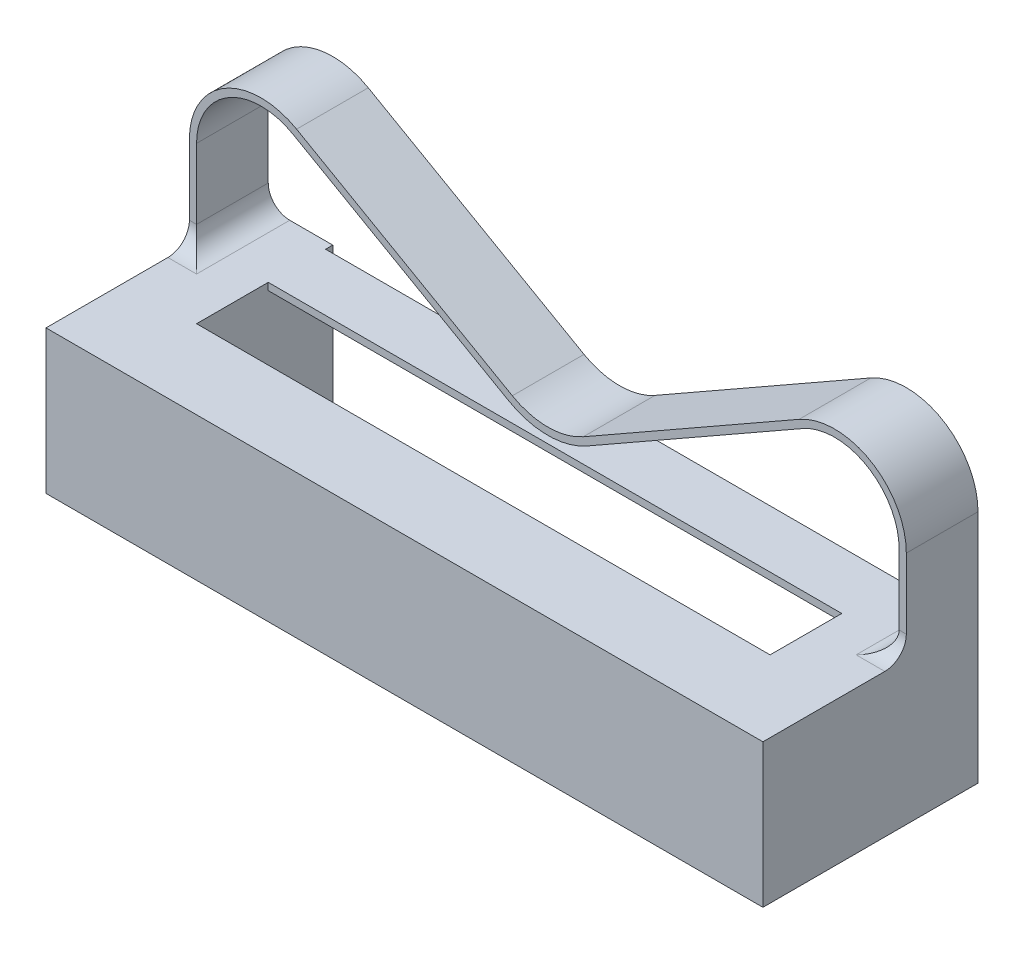
SolidWorks part; units mm, degrees
ref_plane "Front" through (0, 0, 0) normal (0, 0, 1) x (1, 0, 0)
ref_plane "Top" through (0, 0, 0) normal (0, 1, 0) x (1, 0, 0)
ref_plane "Right" through (0, 0, 0) normal (1, 0, 0) x (0, 0, -1)
sketch "Skizze1" plane through (0, 0, 0) normal (0, 0, 1) x (1, 0, 0)
  line L0 (0, 0) -> (100, 0)
  line L1 (0, 0) -> (0, 20)
  line L2 (0, 20) -> (100, 20)
  line L3 (100, 20) -> (100, 0)
  dimension "D1" = 20
  dimension "D2" = 100
extrude "Aufsatz-Linear austragen1" add sketch "Skizze1" along normal blind 50 contours L0 L3 L2 L1
sketch "Skizze3" plane through (0, 0, 0) normal (0, -1, 0) x (1, 0, 0)
  line L0 (0, 25) -> (100, 25) construction
  line L1 (0, 50) -> (0, 0) construction
  line L2 (100, 50) -> (100, 0) construction
  line L3 (50, 50) -> (50, 25) construction
  line L4 (0, 50) -> (100, 50) construction
  line L5 (50, 25) -> (50, 0) construction
  line L6 (0, 0) -> (100, 0) construction
  line L7 (10, 21) -> (90, 11) construction
  line L12 (10, 39) -> (90, 39)
  line L13 (10, 39) -> (10, 29)
  line L14 (10, 29) -> (90, 29)
  line L15 (90, 39) -> (90, 29)
  line L16 (10, 39) -> (90, 29) construction
  line L17 (10, 29) -> (90, 39) construction
  line L18 (10, 11) -> (90, 21) construction
  line L19 (90, 11) -> (90, 21)
  line L20 (10, 21) -> (90, 21)
  line L21 (10, 11) -> (10, 21)
  line L22 (10, 11) -> (90, 11)
  point P10 (50, 34)
  point P22 (50, 16)
  dimension "D1" = 4
  dimension "D2" = 10
  dimension "D3" = 80
extrude "Schnitt-Linear austragen1" cut sketch "Skizze3" against normal through all
sketch "Skizze4" plane through (0, 0, 0) normal (0, -1, 0) x (1, 0, 0)
  line L0 (50, 50) -> (50, 0) construction
  line L1 (0, 50) -> (100, 50) construction
  line L2 (0, 0) -> (100, 0) construction
  line L3 (90, 11) -> (90, 21) construction
  line L4 (10, 34) -> (90, 34)
  line L5 (10, 34) -> (10, 16)
  line L6 (10, 16) -> (90, 16)
  line L7 (90, 34) -> (90, 16)
  line L8 (10, 34) -> (90, 16) construction
  line L9 (10, 16) -> (90, 34) construction
  point P6 (50, 25)
extrude "Schnitt-Linear austragen2" cut sketch "Skizze4" against normal offset from surface (19 mm away) 1 up to face at (50, 20, 34)
ref_plane "Ebene1" through (0, 0, 25) normal (0, 0, 1) x (1, 0, 0)
sketch "Skizze2" plane through (0, 0, 25) normal (0, 0, 1) x (1, 0, 0)
  line L0 (0, 20) -> (0, 32.7896)
  line L1 (50, 0) -> (50, 20) construction
  line L2 (0, 0) -> (100, 0) construction
  line L3 (0, 20) -> (100, 20) construction
  line L4 (100, 20) -> (100, 32.7896)
  line L5 (85.048, 41.4773) -> (54.952, 24.3227)
  line L6 (45.048, 24.3227) -> (14.952, 41.4773)
  arc A0 (54.952, 24.3227) -> (45.048, 24.3227) centre (50, 33.0104) cw
  arc A1 (100, 32.7896) -> (85.048, 41.4773) centre (90, 32.7896) ccw
  arc A2 (14.952, 41.4773) -> (0, 32.7896) centre (10, 32.7896) ccw
  point P19 (50, 21.5)
  point P22 (100, 50)
  point P25 (0, 50)
  dimension "D3" = 10
  dimension "D1" = 30
  dimension "D2" = 1.5
extrude "Linear-Austragen-Dünn1" add sketch "Skizze2" along normal blind 5 and the other way blind 5 thin
sketch "Skizze5" plane through (0, 0, 0) normal (0, 0, -1) x (-1, 0, 0)
  line L1 (-100, 20) -> (0, 20)
  line L2 (-100, 20) -> (-100, 0)
  line L3 (-100, 0) -> (0, 0)
  line L4 (0, 20) -> (0, 0)
extrude "Schnitt-Linear austragen3" cut sketch "Skizze5" against normal up to surface (20 mm away) up to face at (50, 30.2798, 20)
fillet "Verrundung1" radius 3 4 edges at (99.5, 20, 30) (99, 20, 25) (1, 20, 25) (0.5, 20, 30)
